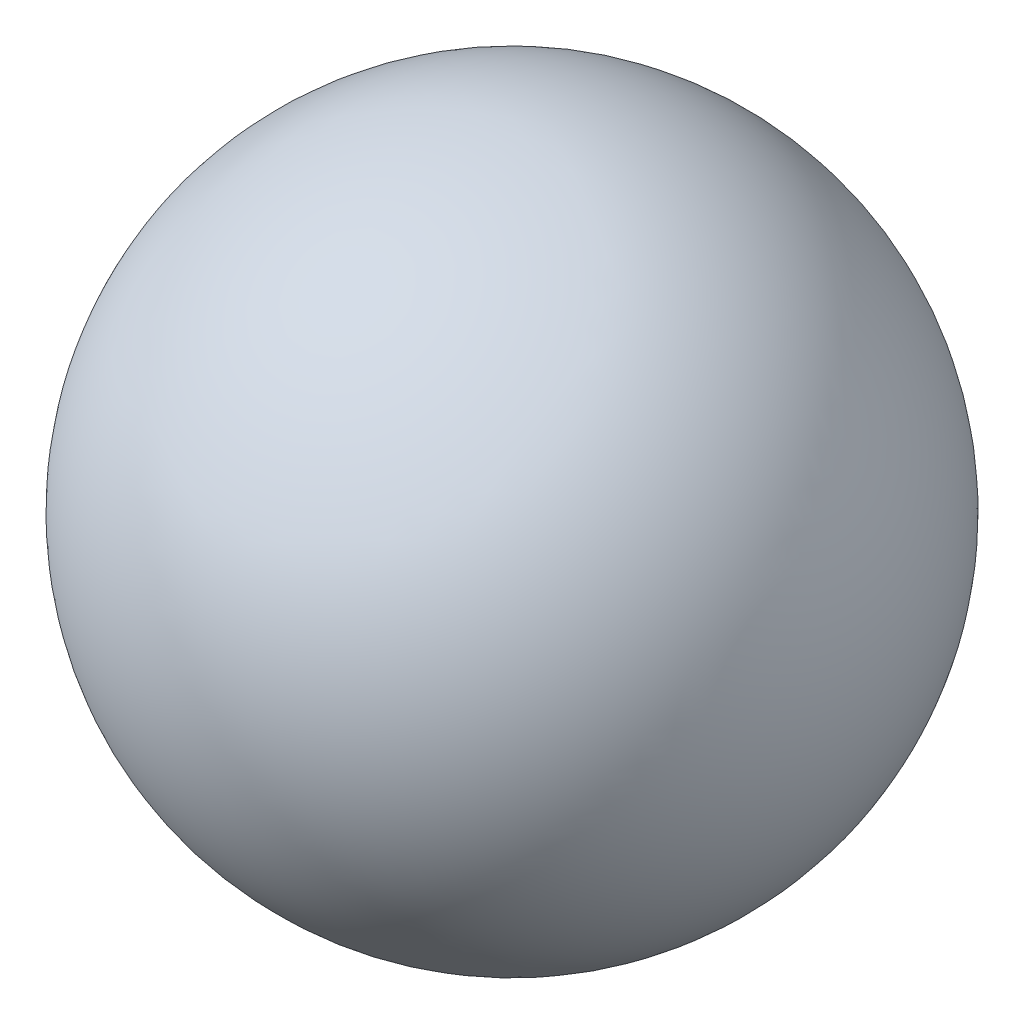
SolidWorks part; units mm, degrees
ref_plane "Front Plane" through (0, 0, 0) normal (0, 0, 1) x (1, 0, 0)
ref_plane "Top Plane" through (0, 0, 0) normal (0, 1, 0) x (1, 0, 0)
ref_plane "Right Plane" through (0, 0, 0) normal (1, 0, 0) x (0, 0, -1)
sketch "Sketch1" plane through (0, 0, 0) normal (0, 0, 1) x (1, 0, 0)
  line L0 (0, 203.2) -> (0, -203.2) construction
  circle A0 centre (0, 0) radius 203.2
  point P5 (0, -203.2)
  dimension "D1" = 406.4
sketch "Sketch2" plane through (0, 0, 0) normal (0, 1, 0) x (1, 0, 0)
  line L0 (-203.2, 0) -> (203.2, 0) construction
  line L1 (-203.2, 0) -> (203.2, 0)
  arc A0 (-203.2, 0) -> (203.2, 0) centre (0, 0) cw
  dimension "D1" = 203.2
revolve "Revolve3" add sketch "Sketch2" angle 360 about L1
